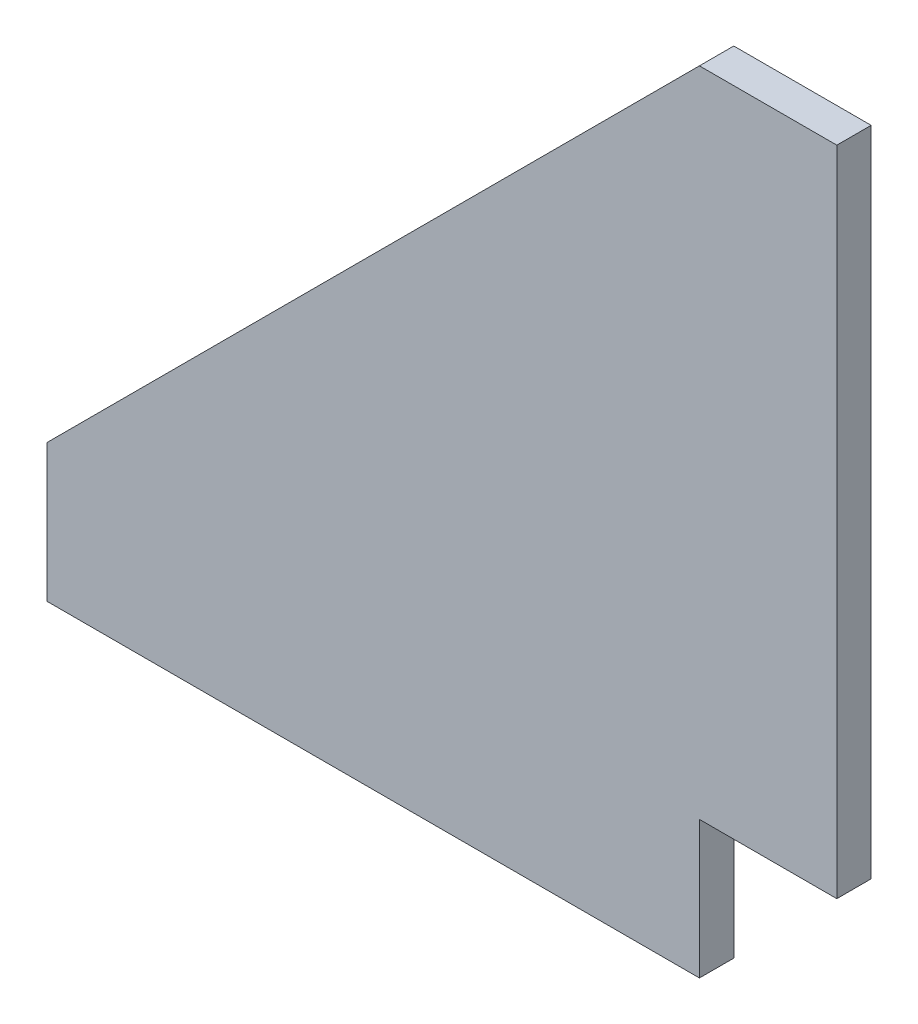
SolidWorks part; units mm, degrees
ref_plane "Front Plane" through (0, 0, 0) normal (0, 0, 1) x (1, 0, 0)
ref_plane "Top Plane" through (0, 0, 0) normal (0, 1, 0) x (1, 0, 0)
ref_plane "Right Plane" through (0, 0, 0) normal (1, 0, 0) x (0, 0, -1)
sketch "Sketch1" plane through (0, 0, 0) normal (0, 0, 1) x (1, 0, 0)
  line L0 (0, 0) -> (120.65, 0)
  line L1 (120.65, 0) -> (120.65, 25.4)
  line L2 (120.65, 25.4) -> (146.05, 25.4)
  line L3 (146.05, 25.4) -> (146.05, 146.05)
  line L5 (146.05, 146.05) -> (120.65, 146.05)
  line L6 (120.65, 146.05) -> (0, 25.4)
  line L7 (0, 25.4) -> (0, 0)
  line L8 (0, 25.4) -> (-25.4, 0) construction
  line L9 (-25.4, 0) -> (0, 0) construction
  dimension "D1" = 25.4
  dimension "D2" = 135
  dimension "D3" = 120.65
  dimension "D4" = 120.65
  dimension "D5" = 25.4
  dimension "D6" = 25.4
  dimension "D7" = 25.4
  dimension "D8" = 120.65
  dimension "D9" = 120.65
extrude "Boss-Extrude1" add sketch "Sketch1" along normal blind 6.35
ref_plane "Plane1" through (0, 0, 3.175) normal (0, 0, -1) x (-1, 0, 0)
ref_plane "Plane2" through (0, 12.7, 0) normal (0, 1, 0) x (1, 0, 0)
